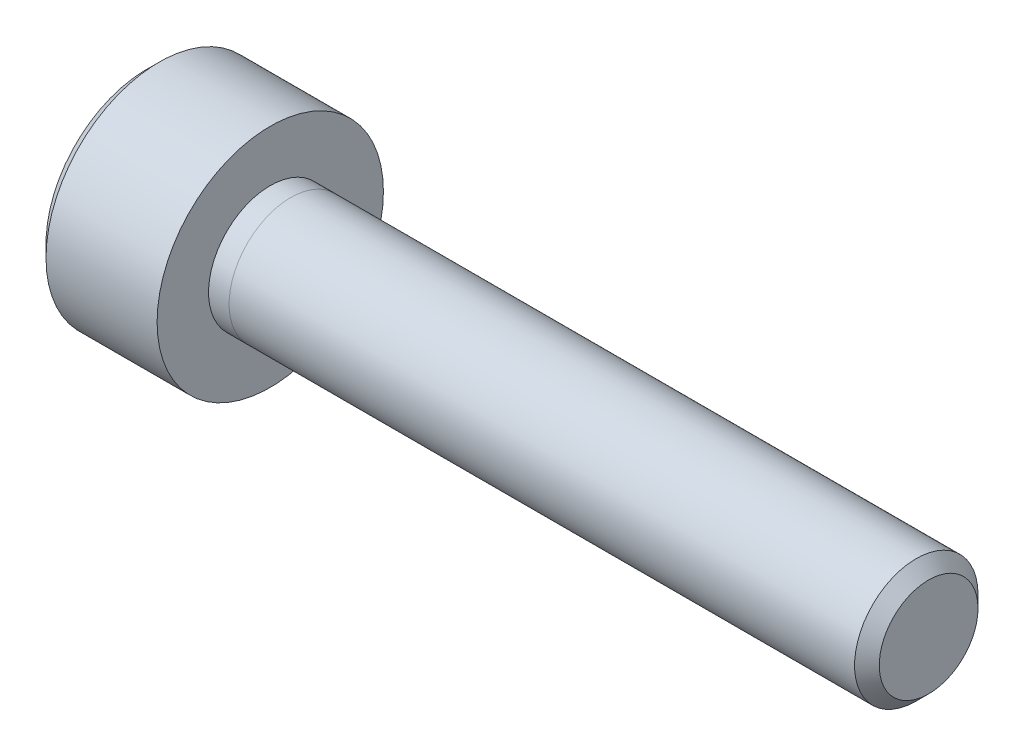
SolidWorks part; units mm, degrees
ref_plane "前视基准面" through (0, 0, 0) normal (0, 0, 1) x (1, 0, 0)
ref_plane "上视基准面" through (0, 0, 0) normal (0, 1, 0) x (1, 0, 0)
ref_plane "右视基准面" through (0, 0, 0) normal (1, 0, 0) x (0, 0, -1)
sketch "草图1" plane through (0, 0, 0) normal (1, 0, 0) x (0, 0, -1)
  circle A0 centre (0, 0) radius 2.75
  dimension "D1" = 5.5
extrude "凸台-拉伸1" add sketch "草图1" along normal blind 3
sketch "草图2" plane through (3, 0, 0) normal (1, 0, 0) x (0, 0, -1)
  circle A0 centre (0, 0) radius 1.5
  dimension "D1" = 3
extrude "凸台-拉伸2" add sketch "草图2" along normal blind 0.5
chamfer "倒角2" distance 0.3 angle 45 1 edges at (0, 0, -2.75)
sketch "草图5" plane through (0, 0, 0) normal (-1, 0, 0) x (0, 0, 1)
  line L1 (1.4307, 0.1905) -> (0.5504, 1.3343)
  line L2 (0.5504, 1.3343) -> (-0.8804, 1.1438)
  line L3 (-0.8804, 1.1438) -> (-1.4307, -0.1905)
  line L4 (-1.4307, -0.1905) -> (-0.5504, -1.3343)
  line L5 (-0.5504, -1.3343) -> (0.8804, -1.1438)
  line L6 (0.8804, -1.1438) -> (1.4307, 0.1905)
  circle A0 centre (0, 0) radius 1.25 construction
  dimension "D1" = 2.5
extrude "切除-拉伸1" cut sketch "草图5" against normal blind 2.2
sketch "草图11" plane through (3.5, 0, 0) normal (1, 0, 0) x (0, 0, -1)
  circle A0 centre (0, 0) radius 1.5
  dimension "D1" = 3
extrude "凸台-拉伸6" add sketch "草图11" along normal blind 15.5 separate body
cosmetic thread "装饰螺纹线3" parameters "D1"=8, "D2"=1.5
chamfer "倒角3" distance 0.3 angle 45 1 edges at (19, 0, -1.5)
